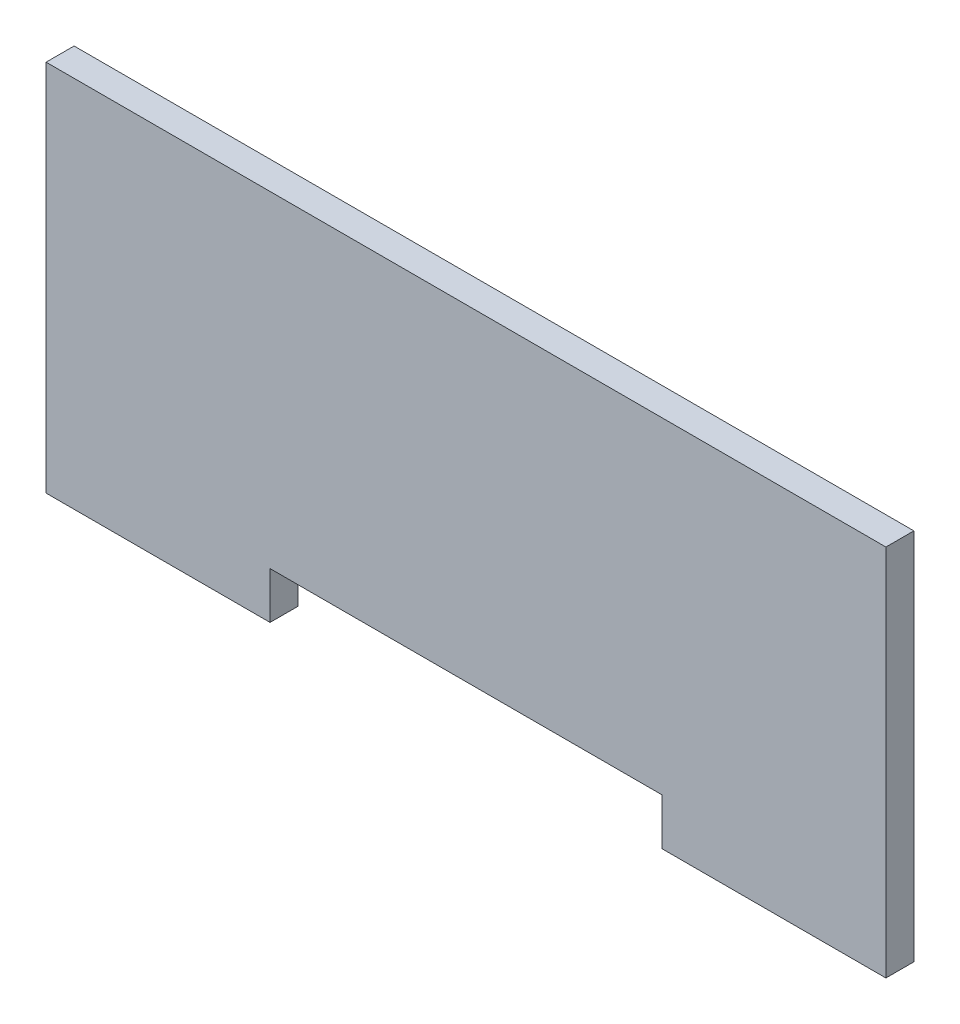
SolidWorks part; units mm, degrees
ref_plane "前视" through (0, 0, 0) normal (0, 0, 1) x (1, 0, 0)
ref_plane "上视" through (0, 0, 0) normal (0, 1, 0) x (1, 0, 0)
ref_plane "右视" through (0, 0, 0) normal (1, 0, 0) x (0, 0, -1)
sketch "草图1" plane through (0, 0, 0) normal (0, 0, 1) x (1, 0, 0)
  line L1 (-22.6948, 30.5659) -> (67.3052, 30.5659)
  line L2 (-22.6948, 30.5659) -> (-22.6948, -9.4341)
  line L3 (-22.6948, -9.4341) -> (1.3052, -9.4341)
  line L4 (67.3052, 30.5659) -> (67.3052, -9.4341)
  line L5 (43.3052, -4.4341) -> (43.3052, -9.4341)
  line L6 (22.3052, 33.3651) -> (22.3052, -21.3108) construction
  line L7 (1.3052, -4.4341) -> (1.3052, -9.4341)
  line L8 (43.3052, -9.4341) -> (67.3052, -9.4341)
  line L9 (1.3052, -4.4341) -> (43.3052, -4.4341)
  dimension "D1" = 24
  dimension "D2" = 40
  dimension "D3" = 42
  dimension "D4" = 5
  dimension "D5" = 24
extrude "凸台-拉伸1" add sketch "草图1" along normal blind 3
